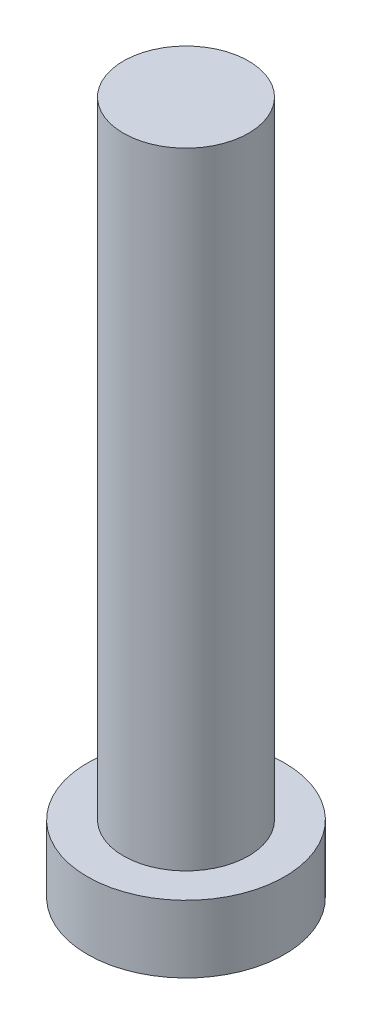
SolidWorks part; units mm, degrees
ref_plane "前视基准面" through (0, 0, 0) normal (0, 0, 1) x (1, 0, 0)
ref_plane "上视基准面" through (0, 0, 0) normal (0, 1, 0) x (1, 0, 0)
ref_plane "右视基准面" through (0, 0, 0) normal (1, 0, 0) x (0, 0, -1)
sketch "草图1" plane through (0, 0, 0) normal (0, 1, 0) x (1, 0, 0)
  circle A0 centre (0, 0) radius 3.15
extrude "凸台-拉伸1" add sketch "草图1" along normal blind 2.15
sketch "草图2" plane through (0, 2.15, 0) normal (0, 1, 0) x (1, 0, 0)
  circle A0 centre (0, 0) radius 2
extrude "凸台-拉伸2" add sketch "草图2" along normal blind 20
sketch "草图3" plane through (0, 0, 0) normal (0, -1, 0) x (1, 0, 0)
  line L0 (-0.5, 1) -> (-0.5, 2)
  line L1 (-2, -0.5) -> (-1, -0.5)
  line L2 (-2, -0.5) -> (-2, 0.5)
  line L3 (-2, 0.5) -> (-1, 0.5)
  line L4 (2, -0.5) -> (2, 0.5)
  line L5 (-2, -0.5) -> (2, 0.5) construction
  line L6 (-2, 0.5) -> (2, -0.5) construction
  line L7 (-0.5, -2) -> (0.5, -2)
  line L8 (-0.5, -2) -> (-0.5, -1)
  line L9 (-0.5, 2) -> (0.5, 2)
  line L10 (0.5, -2) -> (0.5, -1)
  line L11 (-0.5, -2) -> (0.5, 2) construction
  line L12 (-0.5, 2) -> (0.5, -2) construction
  line L13 (1, -0.5) -> (2, -0.5)
  line L14 (0.5, 1) -> (0.5, 2)
  line L15 (1, 0.5) -> (2, 0.5)
  arc A0 (-0.5, -1) -> (-1, -0.5) centre (-1, -1) ccw
  arc A1 (1, -0.5) -> (0.5, -1) centre (1, -1) ccw
  arc A2 (0.5, 1) -> (1, 0.5) centre (1, 1) ccw
  arc A3 (-0.5, 1) -> (-1, 0.5) centre (-1, 1) cw
  point P0 (0, 0)
  point P6 (0, 0)
  point P21 (0.5, 0.5)
  dimension "D1" = 0.5
extrude "切除-拉伸1" cut sketch "草图3" against normal blind 1.5
